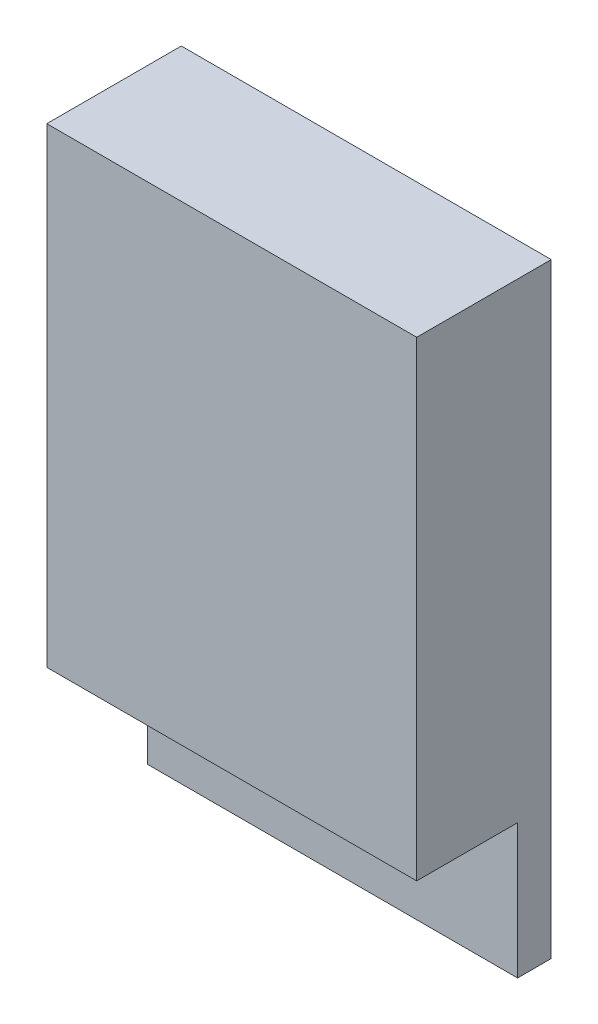
SolidWorks part; units mm, degrees
ref_plane "Front" through (0, 0, 0) normal (0, 0, 1) x (1, 0, 0)
ref_plane "Top" through (0, 0, 0) normal (0, 1, 0) x (1, 0, 0)
ref_plane "Right" through (0, 0, 0) normal (1, 0, 0) x (0, 0, -1)
sketch "Sketch1" plane through (0, 0, 0) normal (0, 0, 1) x (1, 0, 0)
  line L1 (13.97, -22.86) -> (-13.97, -22.86)
  line L2 (13.97, -22.86) -> (13.97, 22.86)
  line L3 (13.97, 22.86) -> (-13.97, 22.86)
  line L4 (-13.97, -22.86) -> (-13.97, 22.86)
  line L5 (13.97, -22.86) -> (-13.97, 22.86) construction
  line L6 (13.97, 22.86) -> (-13.97, -22.86) construction
  point P0 (0, 0)
  dimension "D1" = 45.72
  dimension "D2" = 27.94
extrude "Boss-Extrude1" add sketch "Sketch1" along normal blind 2.54
sketch "Sketch2" plane through (0, 0, 2.54) normal (0, 0, 1) x (1, 0, 0)
  line L0 (13.97, -22.86) -> (13.97, 22.86) construction
  line L1 (-13.97, 22.86) -> (13.97, 22.86)
  line L2 (-13.97, 22.86) -> (-13.97, -12.7)
  line L3 (-13.97, -12.7) -> (13.97, -12.7)
  line L4 (13.97, 22.86) -> (13.97, -12.7)
  dimension "D1" = 35.56
extrude "Boss-Extrude2" add sketch "Sketch2" along normal blind 7.62
